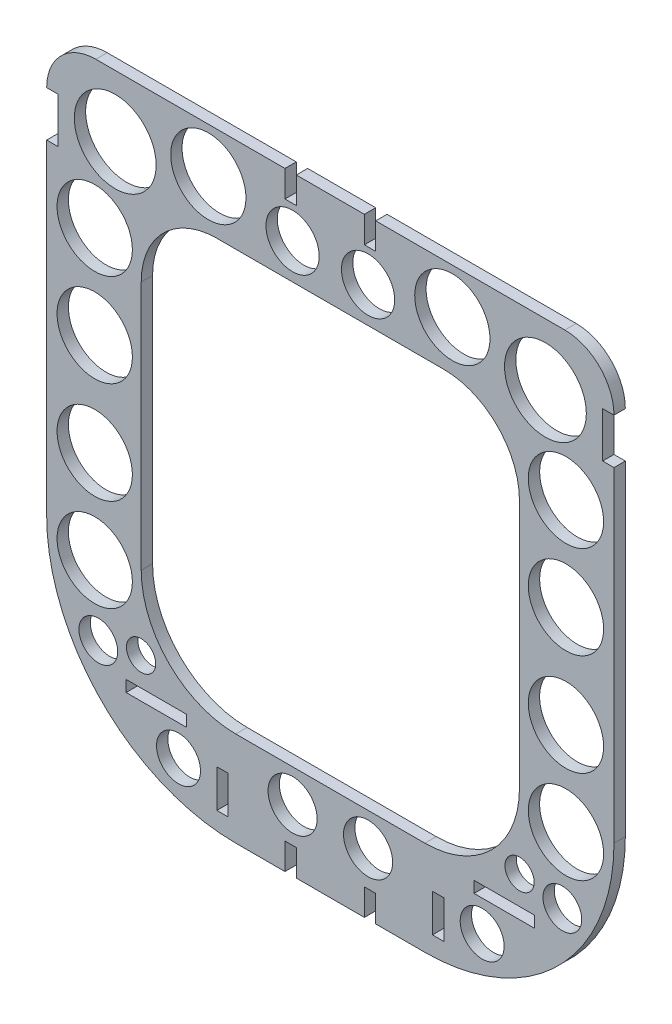
SolidWorks part; units mm, degrees
ref_plane "Front Plane" through (0, 0, 0) normal (0, 0, 1) x (1, 0, 0)
ref_plane "Top Plane" through (0, 0, 0) normal (0, 1, 0) x (1, 0, 0)
ref_plane "Right Plane" through (0, 0, 0) normal (1, 0, 0) x (0, 0, -1)
sketch "Sketch1" plane through (0, 0, 0) normal (0, 0, 1) x (1, 0, 0)
  line L0 (-0.5, -84.19) -> (0.5, -84.19)
  line L1 (75, -34.19) -> (75, 63.81)
  line L2 (-25, -84.19) -> (-0.5, -84.19)
  line L3 (0.5, -84.19) -> (25, -84.19)
  line L4 (62, 76.81) -> (-62, 76.81)
  line L5 (75, 63.81) -> (-75, 63.81) construction
  line L6 (-75, 63.81) -> (-75, -34.19)
  line L7 (50, 51.81) -> (-50, 51.81)
  line L8 (-50, 51.81) -> (-50, -34.19)
  line L9 (-25, -59.19) -> (-0.5, -59.19)
  line L10 (-0.5, -59.19) -> (0.5, -59.19)
  line L11 (0.5, -59.19) -> (25, -59.19)
  line L12 (50, -34.19) -> (50, 51.81)
  arc A0 (25, -84.19) -> (75, -34.19) centre (25, -34.19) ccw
  arc A1 (-75, -34.19) -> (-25, -84.19) centre (-25, -34.19) ccw
  arc A2 (75, 63.81) -> (62, 76.81) centre (62, 63.81) ccw
  arc A3 (-75, 63.81) -> (-62, 76.81) centre (-62, 63.81) cw
  arc A4 (-50, 51.81) -> (-50, 51.81) centre (-50, 51.81) cw
  arc A5 (-50, -34.19) -> (-25, -59.19) centre (-25, -34.19) ccw
  arc A6 (25, -59.19) -> (50, -34.19) centre (25, -34.19) ccw
  arc A7 (50, 51.81) -> (50, 51.81) centre (50, 51.81) ccw
  point P2 (0, 76.81)
  dimension "D1" = 13
  dimension "D2" = 98
  dimension "D3" = 150
  dimension "D4" = 76.81
  dimension "D5" = 25
extrude "Boss-Extrude1" add sketch "Sketch1" along normal blind 3
fillet "Fillet1" radius 20 2 edges at (50, 51.81, 1.5) (-50, 51.81, 1.5)
sketch "Sketch2" plane through (0, 0, 0) normal (0, 0, -1) x (-1, 0, 0)
  line L0 (-62, 76.81) -> (62, 76.81) construction
  line L1 (-12, 76.81) -> (-9, 76.81)
  line L2 (-12, 76.81) -> (-12, 69.81)
  line L3 (-12, 69.81) -> (-9, 69.81)
  line L4 (-9, 76.81) -> (-9, 69.81)
  line L5 (25, -84.19) -> (-25, -84.19) construction
  line L6 (-12, -84.19) -> (-9, -84.19)
  line L7 (-12, -84.19) -> (-12, -77.19)
  line L8 (-12, -77.19) -> (-9, -77.19)
  line L9 (-9, -84.19) -> (-9, -77.19)
  line L10 (0, 1.65) -> (0, -1.65) construction
  line L11 (12, -77.19) -> (9, -77.19)
  line L12 (9, -84.19) -> (9, -77.19)
  line L13 (12, -84.19) -> (9, -84.19)
  line L14 (12, -84.19) -> (12, -77.19)
  line L15 (12, 69.81) -> (9, 69.81)
  line L16 (9, 76.81) -> (9, 69.81)
  line L17 (12, 76.81) -> (9, 76.81)
  line L18 (12, 76.81) -> (12, 69.81)
  line L19 (54, -64.19) -> (38, -64.19)
  line L20 (-54, -61.19) -> (-38, -61.19)
  line L21 (-54, -61.19) -> (-54, -64.19)
  line L22 (-54, -64.19) -> (-38, -64.19)
  line L23 (-38, -61.19) -> (-38, -64.19)
  line L24 (38, -61.19) -> (38, -64.19)
  line L25 (54, -61.19) -> (38, -61.19)
  line L26 (54, -61.19) -> (54, -64.19)
  line L27 (25, -59.19) -> (-25, -59.19) construction
  line L28 (30, -79.19) -> (27, -79.19)
  line L29 (-30, -69.19) -> (-27, -69.19)
  line L30 (-30, -69.19) -> (-30, -79.19)
  line L31 (-30, -79.19) -> (-27, -79.19)
  line L32 (-27, -69.19) -> (-27, -79.19)
  line L33 (27, -69.19) -> (27, -79.19)
  line L34 (30, -69.19) -> (27, -69.19)
  line L35 (30, -69.19) -> (30, -79.19)
  line L36 (-75, -34.19) -> (-75, 63.81) construction
  line L37 (-75, 63.81) -> (-72, 63.81)
  line L38 (-75, 63.81) -> (-75, 51.81)
  line L39 (-75, 51.81) -> (-72, 51.81)
  line L40 (-72, 63.81) -> (-72, 51.81)
  line L41 (75, 51.81) -> (72, 51.81)
  line L42 (72, 63.81) -> (72, 51.81)
  line L43 (75, 63.81) -> (72, 63.81)
  line L44 (75, 63.81) -> (75, 51.81)
  dimension "D1" = 3
  dimension "D2" = 9
  dimension "D3" = 7
  dimension "D4" = 38
  dimension "D5" = 16
  dimension "D6" = 3
  dimension "D7" = 2
  dimension "D8" = 3
  dimension "D9" = 10
  dimension "D10" = 30
  dimension "D11" = 5
  dimension "D12" = 3
  dimension "D13" = 12
extrude "Cut-Extrude1" cut sketch "Sketch2" against normal blind 10
sketch "Sketch3" plane through (0, 0, 0) normal (0, 0, -1) x (-1, 0, 0)
  line L0 (1.65, 0) -> (-1.65, 0) construction
  line L1 (0, 1.65) -> (0, -1.65) construction
  circle A0 centre (-56.8727, 60.5211) radius 10.8164
  circle A1 centre (-62.2968, 38.0273) radius 9.9589
  circle A2 centre (-62.2968, 13.4596) radius 9.9589
  circle A3 centre (-62.2968, -38.0273) radius 9.9589
  circle A4 centre (-62.2968, -13.4596) radius 9.9589
  circle A5 centre (-32.259, 64.888) radius 9.9486
  circle A6 centre (-9.9815, 61.2025) radius 7.0401
  circle A7 centre (-61.3369, -55.9533) radius 5.1256
  circle A8 centre (-9.9815, -67.886) radius 6.4863
  circle A9 centre (-40.143, -72.3385) radius 5.8149
  circle A10 centre (-50.0276, -53.727) radius 3.8663
  circle A11 centre (50.0276, -53.727) radius 3.8663
  circle A12 centre (40.143, -72.3385) radius 5.8149
  circle A13 centre (9.9815, -67.886) radius 6.4863
  circle A14 centre (61.3369, -55.9533) radius 5.1256
  circle A15 centre (9.9815, 61.2025) radius 7.0401
  circle A16 centre (32.259, 64.888) radius 9.9486
  circle A17 centre (62.2968, -13.4596) radius 9.9589
  circle A18 centre (62.2968, -38.0273) radius 9.9589
  circle A19 centre (62.2968, 13.4596) radius 9.9589
  circle A20 centre (62.2968, 38.0273) radius 9.9589
  circle A21 centre (56.8727, 60.5211) radius 10.8164
extrude "Cut-Extrude2" cut sketch "Sketch3" against normal blind 10
